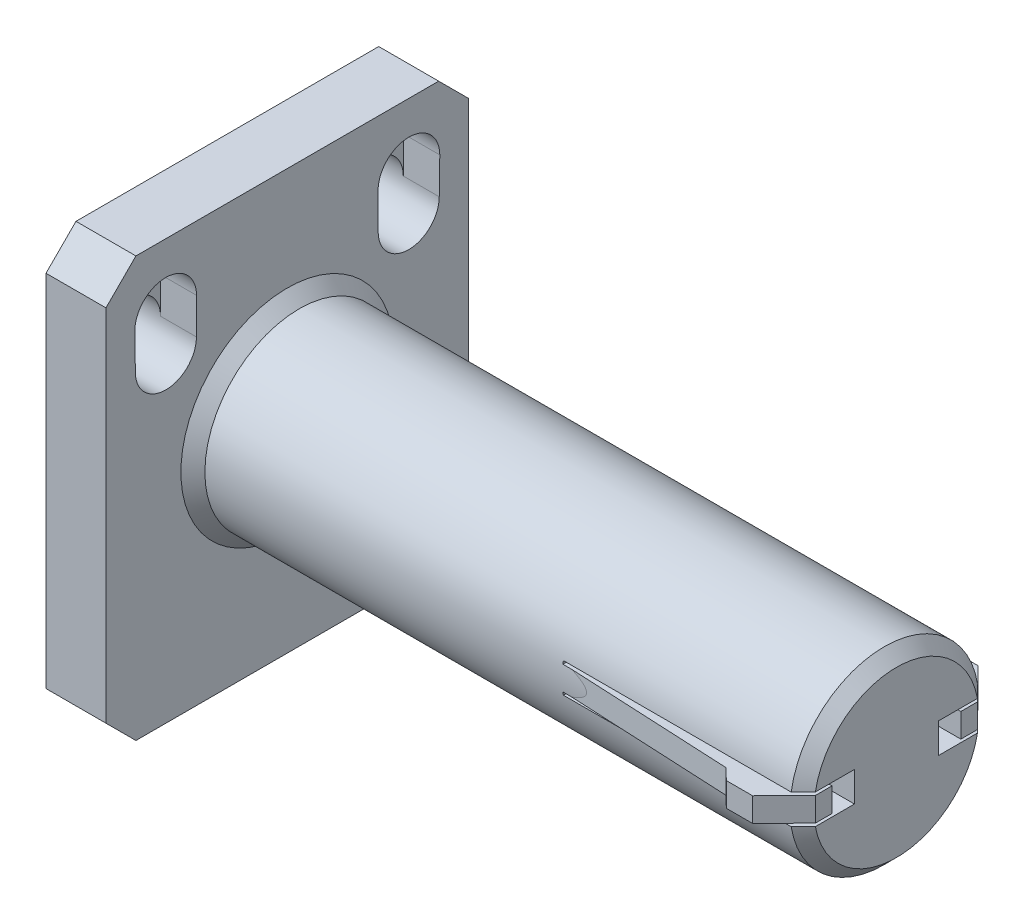
SolidWorks part; units mm, degrees
ref_plane "Front Plane" through (0, 0, 0) normal (0, 0, 1) x (1, 0, 0)
ref_plane "Top Plane" through (0, 0, 0) normal (0, 1, 0) x (1, 0, 0)
ref_plane "Right Plane" through (0, 0, 0) normal (1, 0, 0) x (0, 0, -1)
sketch "Sketch1" plane through (0, 0, 0) normal (1, 0, 0) x (0, 0, -1)
  line L0 (-30.0188, 34.1908) -> (-30.0188, -35.8092)
  line L1 (30.4812, 34.1908) -> (-30.0188, 34.1908)
  line L2 (30.4812, 34.1908) -> (30.4812, -35.8092)
  line L3 (0.2312, 34.1908) -> (0.2312, -35.8092) construction
  line L4 (-17.0695, 23.4402) -> (-17.0695, 21.5935)
  line L5 (-23.0415, 23.4402) -> (-23.0415, 21.5404)
  line L6 (-25.1126, 17.4403) -> (-25.091, 17.9089)
  line L7 (-25.1126, 17.4403) -> (-25.1271, 17.9108)
  line L8 (25.6668, 23.4402) -> (25.575, 17.4403)
  line L9 (15.3689, 23.4402) -> (15.3874, 17.4403)
  line L10 (25.575, 17.4403) -> (25.5895, 17.9108)
  line L11 (25.575, 17.4403) -> (25.5534, 17.9089)
  line L12 (23.5039, 23.4402) -> (23.5039, 21.5404)
  line L13 (17.5319, 23.4402) -> (17.5319, 21.5935)
  line L14 (-14.9066, 23.4402) -> (-14.925, 17.4403)
  line L15 (-25.2045, 23.4402) -> (-25.1126, 17.4403)
  line L16 (-30.0188, -35.8092) -> (30.4812, -35.8092)
  arc A0 (-23.0415, 23.4402) -> (-17.0695, 23.4402) centre (-20.0555, 23.4402) cw
  arc A1 (25.6668, 23.4402) -> (15.3689, 23.4402) centre (20.5179, 23.4402) ccw
  arc A2 (17.5319, 21.5935) -> (23.5039, 21.5404) centre (20.4812, 17.4403) ccw
  arc A3 (23.5039, 23.4402) -> (17.5319, 23.4402) centre (20.5179, 23.4402) ccw
  arc A4 (-17.0695, 21.5935) -> (-23.0415, 21.5404) centre (-20.0188, 17.4403) cw
  arc A5 (-25.2045, 23.4402) -> (-14.9066, 23.4402) centre (-20.0555, 23.4402) cw
  point P29 (0.2312, -3.8092)
  dimension "D1" = 21.2495
  dimension "D2" = 38
extrude "Boss-Extrude1" add sketch "Sketch1" along normal blind 10
sketch "Sketch2" plane through (10, 0, 0) normal (1, 0, 0) x (0, 0, -1)
  line L0 (0.2312, 34.1908) -> (0.2312, -35.8092) construction
  line L1 (30.4812, 34.1908) -> (-30.0188, 34.1908) construction
  line L2 (-30.0188, -35.8092) -> (30.4812, -35.8092) construction
  circle A0 centre (0.2312, -0.8092) radius 15.75
  dimension "D1" = 31.5
extrude "Boss-Extrude2" add sketch "Sketch2" along normal blind 101.6
sketch "Sketch3" plane through (111.6, 0, 0) normal (1, 0, 0) x (0, 0, -1)
  line L0 (-15.5188, -0.8092) -> (15.9812, -0.8092) construction
  line L1 (-15.5188, 1.1908) -> (-10.5188, 1.1908)
  line L2 (-15.5188, -2.8092) -> (-10.5188, -2.8092)
  line L3 (-15.5188, 1.6908) -> (-15.5188, 1.1908)
  line L4 (15.9812, -2.8092) -> (15.9812, -3.3092)
  line L5 (-15.5188, 1.6908) -> (-10.0188, 1.6908)
  line L6 (-15.5188, -3.3092) -> (-10.0188, -3.3092)
  line L7 (-10.0188, 1.6908) -> (-10.0188, -3.3092)
  line L8 (-10.5188, 1.1908) -> (-10.5188, -2.8092)
  line L9 (10.4812, -3.3092) -> (15.9812, -3.3092)
  line L11 (-15.5188, 1.1908) -> (15.9812, 1.1908) construction
  line L12 (-10.5188, 1.6908) -> (-10.5188, -3.3092) construction
  line L13 (0.2312, -0.8092) -> (0.2312, 14.9408) construction
  line L14 (-15.5188, -2.8092) -> (15.9812, -2.8092) construction
  line L15 (10.9812, 1.1908) -> (10.9812, -2.8092)
  line L16 (10.4812, 1.6908) -> (10.4812, -3.3092)
  line L17 (15.9812, 1.6908) -> (15.9812, 1.1908)
  line L18 (15.9812, -2.8092) -> (10.9812, -2.8092)
  line L20 (10.9812, 1.1908) -> (15.9812, 1.1908)
  line L21 (10.4812, 1.6908) -> (15.9812, 1.6908)
  line L22 (-15.5188, -3.3092) -> (15.9812, -3.3092) construction
  line L23 (-15.5188, -2.8092) -> (-15.5188, -3.3092)
  line L24 (-15.5188, 1.6908) -> (15.9812, 1.6908) construction
  circle A0 centre (0.2312, -0.8092) radius 15.75 construction
  circle A1 centre (0.2312, -0.8092) radius 15.75 construction
  dimension "D5" = 5.5
  dimension "D1" = 2
  dimension "D2" = 2
  dimension "D3" = 0.5
  dimension "D4" = 0.5
  dimension "D6" = 0.5
extrude "Cut-Extrude1" cut sketch "Sketch3" against normal blind 40
sketch "Sketch8" plane through (111.6, 0, 0) normal (1, 0, 0) x (0, 0, -1)
  line L0 (10.4812, 1.6908) -> (7.2312, 1.6908)
  line L1 (7.2312, 1.6908) -> (7.2312, -3.3092)
  line L2 (7.2312, -3.3092) -> (10.4812, -3.3092)
  line L3 (10.4812, -3.3092) -> (10.4812, 1.6908)
  line L4 (0.2312, 14.9408) -> (0.2312, -16.5592) construction
  line L5 (-10.0188, -3.3092) -> (-10.0188, 1.6908)
  line L6 (-6.7688, -3.3092) -> (-10.0188, -3.3092)
  line L7 (-6.7688, 1.6908) -> (-6.7688, -3.3092)
  line L8 (-10.0188, 1.6908) -> (-6.7688, 1.6908)
  arc A0 (15.7815, 1.6908) -> (-15.3191, 1.6908) centre (0.2312, -0.8092) ccw construction
  arc A1 (-15.3191, -3.3092) -> (15.7815, -3.3092) centre (0.2312, -0.8092) ccw construction
extrude "Cut-Extrude2" cut sketch "Sketch8" against normal up to surface (40 mm away) up to face at (71.6, -0.8092, -13.2749)
chamfer "Chamfer3" distance 2 angle 45 2 edges at (111.6, 14.9408, -0.2312) (111.6, -16.5592, -0.2312)
sketch "Sketch19" plane through (0, 0, 0) normal (-1, 0, 0) x (0, 0, 1)
  line L0 (-25.575, 17.4403) -> (-25.5534, 17.9089) construction
  line L1 (-25.575, 17.4403) -> (-25.5895, 17.9108) construction
  line L2 (-25.6668, 23.4402) -> (-25.575, 17.4403) construction
  line L3 (-15.3689, 23.4402) -> (-15.3874, 17.4403) construction
  line L4 (14.9066, 23.4402) -> (14.925, 17.4403) construction
  line L5 (25.2045, 23.4402) -> (25.1126, 17.4403) construction
  line L6 (25.1126, 17.4403) -> (25.1271, 17.9108) construction
  line L7 (25.1126, 17.4403) -> (25.091, 17.9089) construction
  line L8 (-17.5319, 23.4402) -> (-17.5319, 21.5935) construction
  line L9 (-23.5039, 23.4402) -> (-23.5039, 21.5404) construction
  line L10 (17.0695, 23.4402) -> (17.0695, 21.5935) construction
  line L11 (23.0415, 23.4402) -> (23.0415, 21.5404) construction
  line L12 (30.0188, 34.1908) -> (30.0188, -35.8092) construction
  line L13 (-30.4812, 34.1908) -> (30.0188, 34.1908) construction
  line L14 (-30.4812, 34.1908) -> (-30.4812, -35.8092) construction
  line L15 (30.0188, -35.8092) -> (-30.4812, -35.8092) construction
  line L16 (-25.575, 17.4403) -> (-25.5534, 17.9089)
  line L17 (-25.575, 17.4403) -> (-25.5895, 17.9108)
  line L18 (-25.6668, 23.4402) -> (-25.575, 17.4403)
  line L19 (-15.3689, 23.4402) -> (-15.3874, 17.4403)
  line L20 (14.9066, 23.4402) -> (14.925, 17.4403)
  line L21 (25.2045, 23.4402) -> (25.1126, 17.4403)
  line L22 (25.1126, 17.4403) -> (25.1271, 17.9108)
  line L23 (25.1126, 17.4403) -> (25.091, 17.9089)
  line L24 (-17.5319, 23.4402) -> (-17.5319, 21.5935)
  line L25 (-23.5039, 23.4402) -> (-23.5039, 21.5404)
  line L26 (17.0695, 23.4402) -> (17.0695, 21.5935)
  line L27 (23.0415, 23.4402) -> (23.0415, 21.5404)
  line L28 (30.0188, 34.1908) -> (30.0188, -35.8092)
  line L29 (-30.4812, 34.1908) -> (30.0188, 34.1908)
  line L30 (-30.4812, 34.1908) -> (-30.4812, -35.8092)
  line L31 (30.0188, -35.8092) -> (-30.4812, -35.8092)
  arc A0 (-15.3689, 23.4402) -> (-25.6668, 23.4402) centre (-20.5179, 23.4402) ccw construction
  arc A1 (25.2045, 23.4402) -> (14.9066, 23.4402) centre (20.0555, 23.4402) ccw construction
  arc A2 (-23.5039, 21.5404) -> (-17.5319, 21.5935) centre (-20.4812, 17.4403) ccw construction
  arc A3 (-17.5319, 23.4402) -> (-23.5039, 23.4402) centre (-20.5179, 23.4402) ccw construction
  arc A4 (17.0695, 21.5935) -> (23.0415, 21.5404) centre (20.0188, 17.4403) ccw construction
  arc A5 (23.0415, 23.4402) -> (17.0695, 23.4402) centre (20.0555, 23.4402) ccw construction
  arc A6 (-15.3689, 23.4402) -> (-25.6668, 23.4402) centre (-20.5179, 23.4402) ccw
  arc A7 (25.2045, 23.4402) -> (14.9066, 23.4402) centre (20.0555, 23.4402) ccw
  arc A8 (-23.5039, 21.5404) -> (-17.5319, 21.5935) centre (-20.4812, 17.4403) ccw
  arc A9 (-17.5319, 23.4402) -> (-23.5039, 23.4402) centre (-20.5179, 23.4402) ccw
  arc A10 (17.0695, 21.5935) -> (23.0415, 21.5404) centre (20.0188, 17.4403) ccw
  arc A11 (23.0415, 23.4402) -> (17.0695, 23.4402) centre (20.0555, 23.4402) ccw
  line M5 (25.2045, 23.4402) -> (25.1126, 17.4403)
  line M7 (14.925, 17.4403) -> (14.9066, 23.4402)
  arc M8 (14.9066, 23.4402) -> (25.2045, 23.4402) centre (20.0555, 23.4402) cw
  line M10 (-25.575, 17.4403) -> (-25.6668, 23.4402)
  arc M11 (-25.6668, 23.4402) -> (-15.3689, 23.4402) centre (-20.5179, 23.4402) cw
  line M12 (-15.3689, 23.4402) -> (-15.3874, 17.4403)
extrude "Boss-Extrude9" add sketch "Sketch19" against normal blind 4 contours A9 L24 A8 L25 M12 M11 M10 | A11 L27 A10 L26 M5 M8 M7
sketch "Sketch23" plane through (0, 1.1908, 0) normal (0, 1, 0) x (1, 0, 0)
  line L0 (101.7595, 18.7651) -> (102.5672, 19.5291) construction
  line L1 (111.6, 15.7815) -> (111.6, 18.0291) construction
  line L2 (71.6, 15.7815) -> (100.0846, 17.181)
  line L3 (111.6, 15.7815) -> (111.6, 19.0291)
  line L4 (71.6, 15.7815) -> (111.6, 15.7815)
  line L5 (111.6, 0.2312) -> (65.116, 0.2312) construction
  line L6 (71.6, 15.7815) -> (102.3872, 17.2942) construction
  line L7 (100.0846, -16.7187) -> (102.0386, -18.5667)
  line L8 (111.6, -13.2896) -> (111.6, 13.752) construction
  line L9 (102.0386, -18.5667) -> (111.6, -18.5667)
  line L10 (71.6, -15.3191) -> (111.6, -15.3191)
  line L11 (111.6, -15.3191) -> (111.6, -18.5667)
  line L12 (71.6, -15.3191) -> (100.0846, -16.7187)
  line L13 (102.5672, 19.5291) -> (113.1, 19.5291) construction
  line L14 (102.7662, 19.0291) -> (111.1, 19.0291) construction
  line L16 (111.6, 10.9812) -> (111.6, 15.8537) construction
  line L17 (100.0846, 17.181) -> (102.5672, 19.5291) construction
  line L18 (111.6, 15.7815) -> (111.6, 19.5291) construction
  line L20 (102.0386, 19.0291) -> (111.6, 19.0291)
  line L21 (100.0846, 17.181) -> (102.0386, 19.0291)
  line L26 (10.504, 14.2815) -> (101.7595, 18.7651) construction
  line L27 (113.1, 14.2815) -> (113.1, 19.5291) construction
  line L28 (10.504, 14.2815) -> (109.6, 14.2815) construction
  line L29 (109.7698, 14.2815) -> (113.1, 14.2815) construction
  line L30 (109.6, 14.2815) -> (109.7698, 14.2815) construction
  line L31 (109.6, 15.7815) -> (109.7698, 15.7815) construction
  line L32 (71.6, 15.7815) -> (109.6, 15.7815) construction
  line L33 (103.1642, 18.0291) -> (111.6, 18.0291) construction
  line L34 (102.3872, 17.2942) -> (103.1642, 18.0291) construction
  line L35 (109.7698, 15.7815) -> (111.6, 15.7815) construction
  line L42 (91.9653, 16.2815) -> (111.1, 16.2815) construction
  line L43 (91.9653, 16.2815) -> (100.2939, 16.6907) construction
  line L44 (100.2939, 16.6907) -> (102.7662, 19.0291) construction
  line L45 (111.1, 16.2815) -> (111.1, 19.0291) construction
  line L46 (102.5672, 19.5291) -> (111.6, 19.5291) construction
  dimension "D1" = 1.5
  dimension "D3" = 0.5
extrude "Boss-Extrude10" add sketch "Sketch23" against normal blind 4
chamfer "Chamfer4" distance 5 angle 45 4 edges at (5, 34.1908, -30.4812) (5, -35.8092, -30.4812) (5, -35.8092, 30.0188) (5, 34.1908, 30.0188)
sketch "Sketch28" plane through (0, 1.1908, 0) normal (0, 1, 0) x (1, 0, 0)
  line L0 (111.6, 13.752) -> (105.0705, 20.3921)
  line L1 (105.0705, 20.3921) -> (111.6, 20.3921)
  line L2 (111.6, 20.3921) -> (111.6, 13.752)
  line L3 (111.6, 0.2312) -> (86.3156, 0.2312) construction
  line L4 (111.6, -13.2896) -> (111.6, 13.752) construction
  line L5 (111.6, -19.9298) -> (111.6, -13.2896)
  line L6 (105.0705, -19.9298) -> (111.6, -19.9298)
  line L7 (111.6, -13.2896) -> (105.0705, -19.9298)
extrude "Cut-Extrude9" cut sketch "Sketch28" against normal blind 4
chamfer "Chamfer6" distance 2 angle 45 1 edges at (10, -0.8092, -15.9812)
